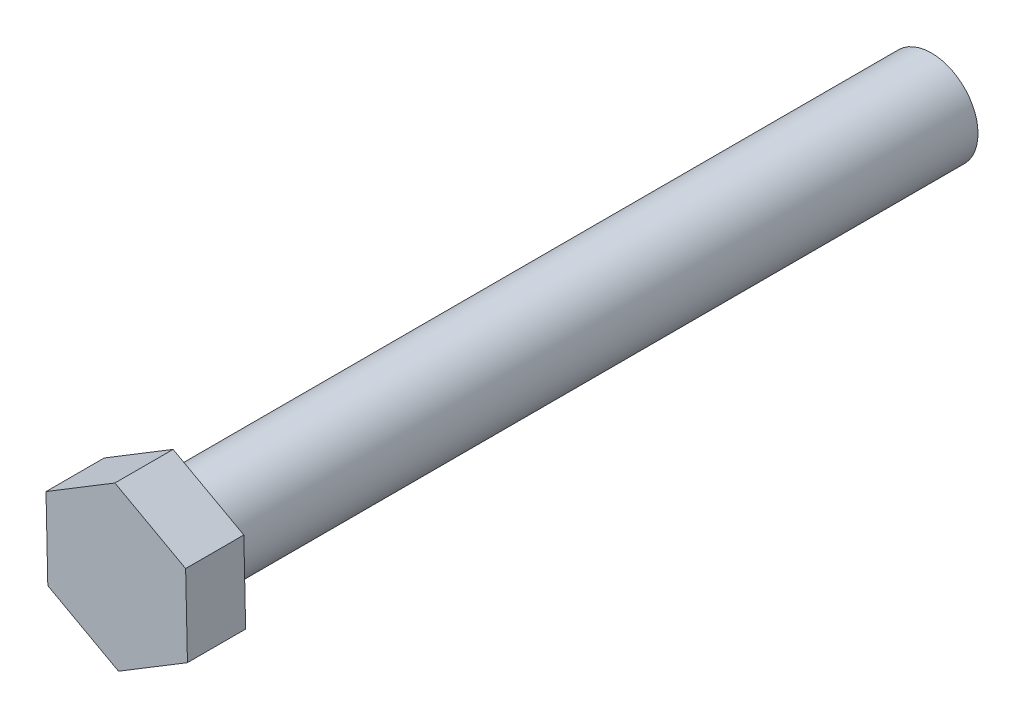
SolidWorks part; units mm, degrees
ref_plane "前视基准面" through (0, 0, 0) normal (0, 0, 1) x (1, 0, 0)
ref_plane "上视基准面" through (0, 0, 0) normal (0, 1, 0) x (1, 0, 0)
ref_plane "右视基准面" through (0, 0, 0) normal (1, 0, 0) x (0, 0, -1)
sketch "草图1" plane through (0, 0, 0) normal (0, 0, 1) x (1, 0, 0)
  circle A0 centre (0, 0) radius 4
  dimension "D1" = 8
extrude "凸台-拉伸1" add sketch "草图1" along normal blind 65
sketch "草图2" plane through (0, 0, 65) normal (0, 0, 1) x (1, 0, 0)
  line L1 (6.0764, -3.3283) -> (5.9206, 3.5981)
  line L2 (5.9206, 3.5981) -> (-0.1558, 6.9265)
  line L3 (-0.1558, 6.9265) -> (-6.0764, 3.3283)
  line L4 (-6.0764, 3.3283) -> (-5.9206, -3.5981)
  line L5 (-5.9206, -3.5981) -> (0.1558, -6.9265)
  line L6 (0.1558, -6.9265) -> (6.0764, -3.3283)
  circle A0 centre (0, 0) radius 6 construction
  dimension "D1" = 12
extrude "凸台-拉伸2" add sketch "草图2" along normal blind 5
